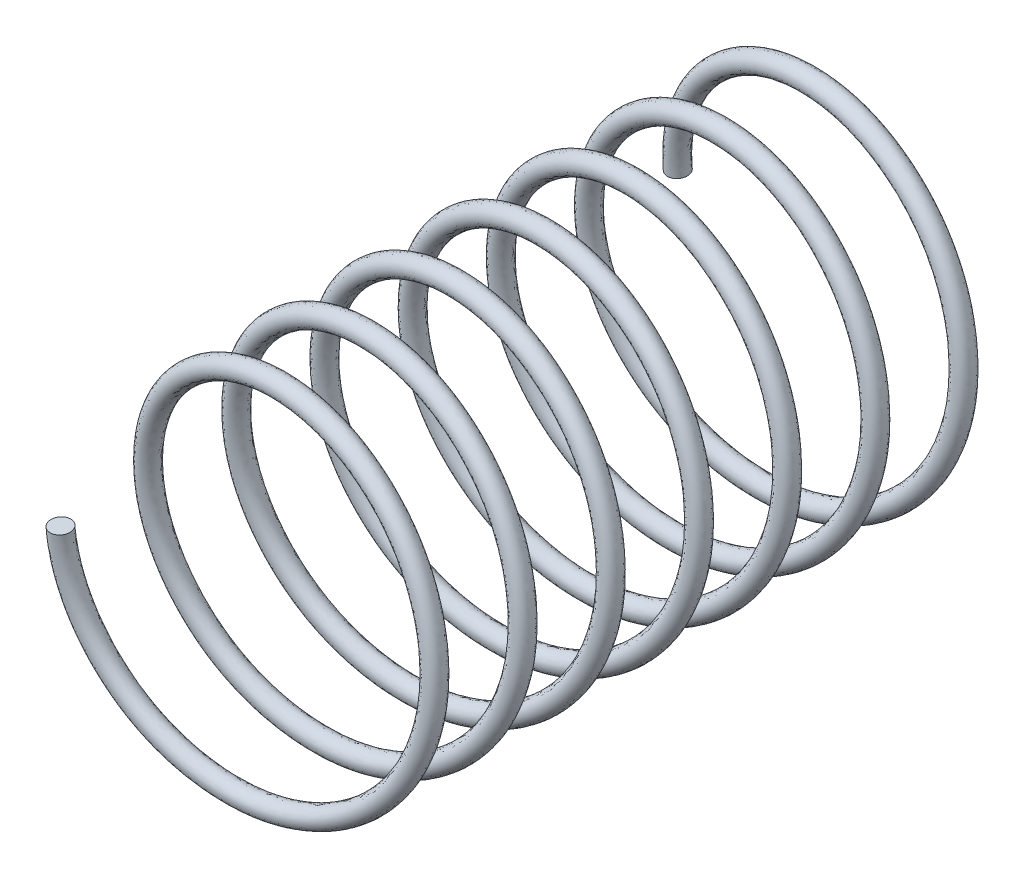
SolidWorks part; units mm, degrees
ref_plane "Front Plane" through (0, 0, 0) normal (0, 0, 1) x (1, 0, 0)
ref_plane "Top Plane" through (0, 0, 0) normal (0, 1, 0) x (1, 0, 0)
ref_plane "Right Plane" through (0, 0, 0) normal (1, 0, 0) x (0, 0, -1)
sketch "Sketch2" plane through (0, 0, 0) normal (0, 0, 1) x (1, 0, 0)
  circle A0 centre (0, 0) radius 2
  dimension "D1" = 4
curve "Helix/Spiral1" pitch 1.0714 height 7.5 turns 7
sweep "Sweep1" add path "Helix/Spiral1" circular profile diameter 0.25 parameters "D3"=0.25
